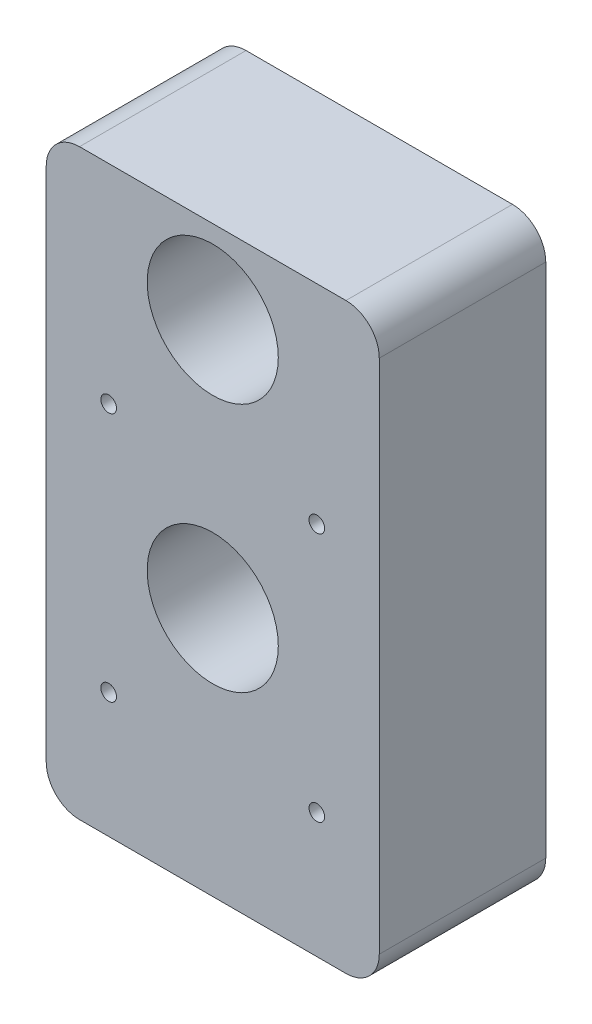
SolidWorks part; units mm, degrees
ref_plane "Front Plane" through (0, 0, 0) normal (0, 0, 1) x (1, 0, 0)
ref_plane "Top Plane" through (0, 0, 0) normal (0, 1, 0) x (1, 0, 0)
ref_plane "Right Plane" through (0, 0, 0) normal (1, 0, 0) x (0, 0, -1)
sketch "Sketch1" plane through (0, 0, 0) normal (0, 0, 1) x (1, 0, 0)
  line L0 (0, 0) -> (0, 31.75) construction
  line L6 (-12.7, 76.2) -> (12.7, 76.2)
  line L7 (-12.7, 76.2) -> (-12.7, 31.75)
  line L8 (-12.7, 31.75) -> (12.7, 31.75)
  line L9 (12.7, 76.2) -> (12.7, 31.75)
  line L10 (5, 76.2) -> (10, 76.2) construction
  dimension "D1" = 44.45
  dimension "D2" = 25.4
extrude "Boss-Extrude1" add sketch "Sketch1" along normal blind 12.7
sketch "Sketch2" plane through (0, 0, 12.7) normal (0, 0, 1) x (1, 0, 0)
  circle A0 centre (0, 50.8) radius 2.75
  circle A1 centre (0, 69.85) radius 2.75
  dimension "D1" = 5.5
extrude "Cut-Extrude1" cut sketch "Sketch2" against normal through all
sketch "Sketch3" plane through (0, 0, 12.7) normal (0, 0, 1) x (1, 0, 0)
  circle A0 centre (0, 50.8) radius 5
  circle A1 centre (0, 69.85) radius 5
  dimension "D1" = 10
extrude "Cut-Extrude2" cut sketch "Sketch3" against normal offset from surface (9.525 mm away) 3.175 up to face at (2.75, 50.8, 0)
sketch "Sketch5" plane through (0, 0, 12.7) normal (0, 0, 1) x (1, 0, 0)
  circle A0 centre (7.9375, 41.275) radius 0.5953
  circle A1 centre (-7.9375, 41.275) radius 0.5953
  circle A2 centre (-7.9375, 60.325) radius 0.5953
  circle A3 centre (7.9375, 60.325) radius 0.5953
  dimension "D1" = 1.1906
extrude "Cut-Extrude3" cut sketch "Sketch5" against normal through all
fillet "Fillet1" radius 2.54 4 edges at (-12.7, 31.75, 6.35) (12.7, 31.75, 6.35) (-12.7, 76.2, 6.35) (12.7, 76.2, 6.35)
